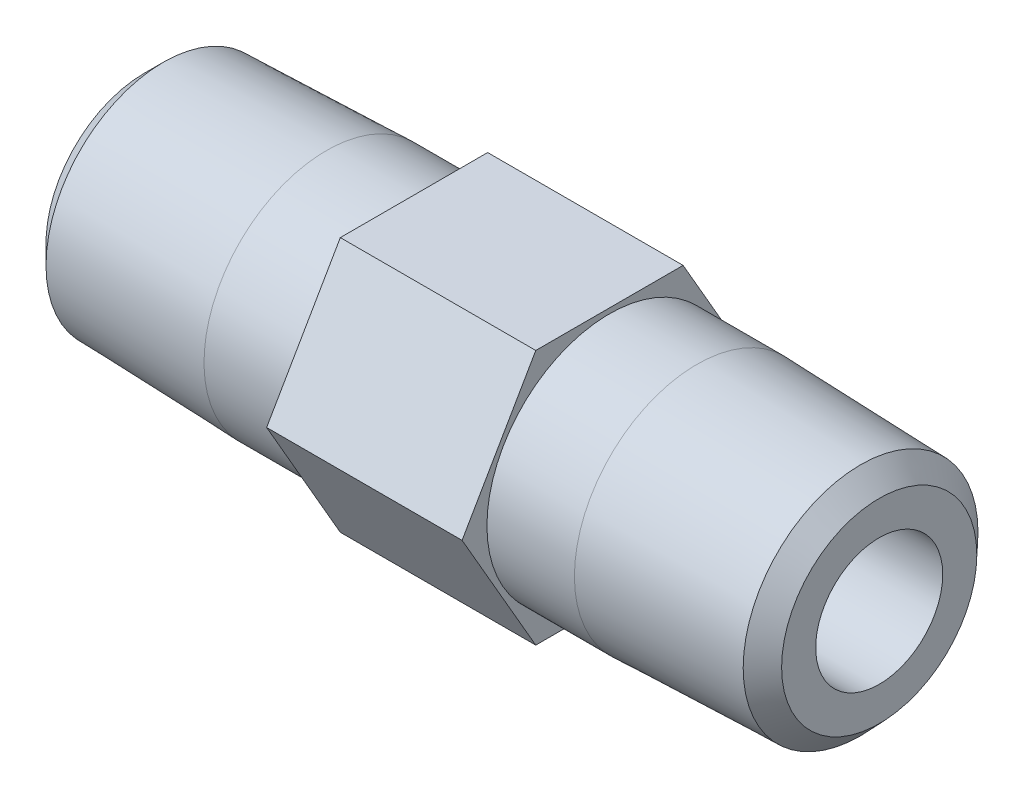
SolidWorks part; units mm, degrees
ref_plane "Front Plane" through (0, 0, 0) normal (0, 0, 1) x (1, 0, 0)
ref_plane "Top Plane" through (0, 0, 0) normal (0, 1, 0) x (1, 0, 0)
ref_plane "Right Plane" through (0, 0, 0) normal (1, 0, 0) x (0, 0, -1)
ref_plane "Plane1" through (15.1028, 0, 0) normal (-1, 0, 0) x (0, -1, 0)
sketch "Sketch1" plane through (15.1028, 0, 0) normal (-1, 0, 0) x (0, -1, 0)
  line L0 (7.1437, -4.1244) -> (7.1437, 4.1244)
  line L1 (7.1437, 4.1244) -> (0, 8.2489)
  line L2 (0, 8.2489) -> (-7.1438, 4.1244)
  line L3 (-7.1438, 4.1244) -> (-7.1438, -4.1244)
  line L4 (-7.1438, -4.1244) -> (0, -8.2489)
  line L5 (0, -8.2489) -> (7.1437, -4.1244)
extrude "Boss-Extrude1" add sketch "Sketch1" against normal blind 10.9423
ref_plane "Plane2" through (0, 0, 0) normal (0, 0, -1) x (-1, 0, 0)
sketch "Sketch2" plane through (0, 0, 0) normal (0, 0, -1) x (-1, 0, 0)
  line L0 (-41.148, 6.5402) -> (-41.148, 0)
  line L1 (-41.148, 0) -> (-26.0452, 0)
  line L2 (-26.0452, 0) -> (-26.0452, 6.858)
  line L3 (-26.0452, 6.858) -> (-30.9423, 6.858)
  line L4 (-30.9423, 6.858) -> (-41.148, 6.5402)
  line L5 (-41.148, 0) -> (-26.0452, 0) construction
revolve "Revolve1" add sketch "Sketch2" angle 360 about L5
sketch "Sketch3" plane through (0, 0, 0) normal (0, 0, -1) x (-1, 0, 0)
  line L0 (-15.1028, 6.858) -> (-15.1028, 0)
  line L1 (-15.1028, 0) -> (0, 0)
  line L2 (0, 0) -> (0, 6.5402)
  line L3 (0, 6.5402) -> (-10.2057, 6.858)
  line L4 (-10.2057, 6.858) -> (-15.1028, 6.858)
  line L5 (-15.1028, 0) -> (0, 0) construction
revolve "Revolve2" add sketch "Sketch3" angle 360 about L5
hole_wizard "1/4 Clearance Hole1" positions "Sketch5" profile "Sketch4" hole size "1/4" standard "ANSI Inch"
sketch "Sketch5" plane through (41.148, 0, 0) normal (1, 0, 0) x (0, 0, -1)
  point P0 (0, 0)
sketch "Sketch4" plane through (41.148, 0, 0) normal (0, 1, 0) x (0, 0, -1)
  line L0 (0, 0) -> (0, 15.1028)
  line L1 (0, 15.1028) -> (3.556, 15.1028)
  line L2 (3.556, 15.1028) -> (3.556, 0)
  line L5 (3.556, 0) -> (0, 0)
  line L10 (0, 15.1028) -> (-3.556, 15.1028) construction
  line L11 (0, -6.35) -> (0, 107.95) construction
  dimension "Hole Dia." = 7.112
  dimension "Hole Depth" = 15.1028
  dimension "Drill Angle" = 180
hole_wizard "1/4 Clearance Hole2" positions "Sketch7" profile "Sketch6" hole size "1/4" standard "ANSI Inch"
sketch "Sketch7" plane through (0, 0, 0) normal (-1, 0, 0) x (0, 0, 1)
  point P0 (0, 0)
sketch "Sketch6" plane through (0, 0, 0) normal (0, 1, 0) x (0, 0, 1)
  line L0 (0, 0) -> (0, 15.1028)
  line L1 (0, 15.1028) -> (3.556, 15.1028)
  line L2 (3.556, 15.1028) -> (3.556, 0)
  line L5 (3.556, 0) -> (0, 0)
  line L10 (0, 15.1028) -> (-3.556, 15.1028) construction
  line L11 (0, -6.35) -> (0, 107.95) construction
  dimension "Hole Dia." = 7.112
  dimension "Hole Depth" = 15.1028
  dimension "Drill Angle" = 180
chamfer "Chamfer1" distance 1.0424 angle 45 2 edges at (41.148, 0, 6.5402) (0, -6.5402, 0)
